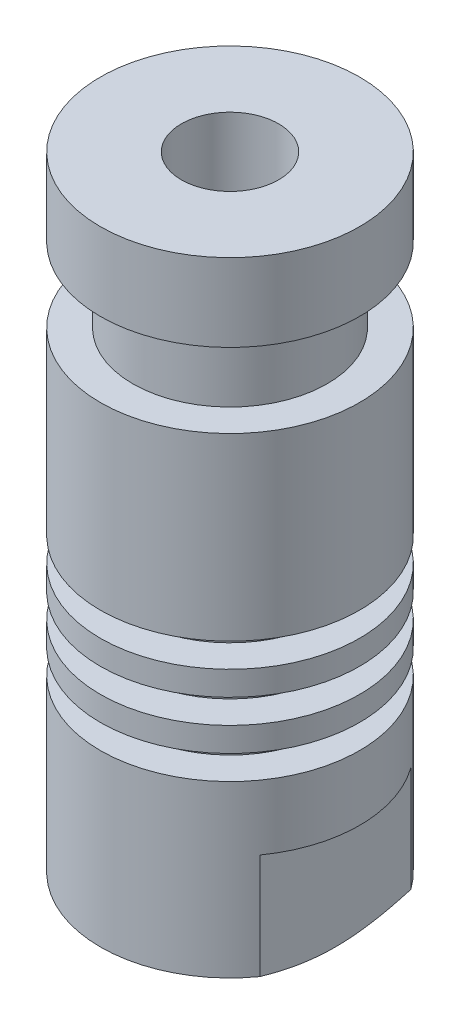
SolidWorks part; units mm, degrees
material "Gomma"
ref_plane "Piano frontale" through (0, 0, 0) normal (0, 0, 1) x (1, 0, 0)
ref_plane "Piano superiore" through (0, 0, 0) normal (0, 1, 0) x (1, 0, 0)
ref_plane "Piano destro" through (0, 0, 0) normal (1, 0, 0) x (0, 0, -1)
sketch "Schizzo1" plane through (0, 0, 0) normal (0, 0, 1) x (1, 0, 0)
  line L0 (0, 0) -> (-5, 0)
  line L1 (-5, 0) -> (-8, 1.5)
  line L2 (-8, 1.5) -> (-8, 12)
  line L3 (-8, 12) -> (-6, 12)
  line L4 (-6, 12) -> (-6, 13.5)
  line L5 (-6, 13.5) -> (-8, 13.5)
  line L6 (-8, 13.5) -> (-8, 15)
  line L7 (-8, 15) -> (-6, 15)
  line L8 (-6, 15) -> (-6, 16.5)
  line L9 (-6, 16.5) -> (-8, 16.5)
  line L10 (-8, 16.5) -> (-8, 18)
  line L11 (-8, 18) -> (-6, 18)
  line L12 (-6, 18) -> (-6, 19.5)
  line L13 (-6, 19.5) -> (-8, 19.5)
  line L14 (-8, 19.5) -> (-8, 30.6)
  line L15 (-8, 30.6) -> (-6, 30.6)
  line L16 (-6, 30.6) -> (-6, 35.2)
  line L17 (-6, 35.2) -> (-8, 35.2)
  line L18 (-8, 35.2) -> (-8, 40)
  line L19 (-8, 40) -> (0, 40)
  line L20 (0, 40) -> (0, 0)
  line L21 (0, 129.4074) -> (0, -17.2322) construction
  dimension "D1" = 1.5
  dimension "D2" = 16
  dimension "D3" = 2
  dimension "D4" = 40
  dimension "D5" = 12
  dimension "D6" = 4.8
  dimension "D7" = 4.6
  dimension "D8" = 1.5
  dimension "D9" = 6
  dimension "D10" = 10
revolve "Rivoluzione1" add sketch "Schizzo1" angle 360 about L21
sketch "Schizzo2" plane through (0, 0, 0) normal (0, 0, 1) x (1, 0, 0)
  line L0 (-8, 8) -> (-6.5, 8)
  line L1 (-6.5, 8) -> (-6.5, 0)
  line L2 (-6.5, 0) -> (-8, 0)
  line L3 (-8, 0) -> (-8, 8)
  line L4 (6.5, 8) -> (6.5, 0)
  line L5 (6.5, 0) -> (8, 0)
  line L6 (8, 0) -> (8, 8)
  line L7 (8, 8) -> (6.5, 8)
  line L8 (0, 0) -> (0, 9.0399) construction
  line L9 (-5, 0) -> (5, 0) construction
  line L10 (8, 40) -> (-8, 40) construction
  line L11 (8, 1.5) -> (8, 12) construction
  line L12 (-8, 12) -> (-8, 1.5) construction
  dimension "D1" = 32
  dimension "D2" = 1.5
extrude "Taglio-Estrusione1" cut sketch "Schizzo2" against normal up to next and the other way up to next
sketch "Schizzo7" plane through (0, 40, 0) normal (0, 1, 0) x (1, 0, 0)
  circle A0 centre (0, 0) radius 3
extrude "Taglio-Estrusione2" cut sketch "Schizzo7" against normal through all
hole_wizard "Foro filettato M8-1" positions "Schizzo9" profile "Schizzo8" tap size "M8" standard "ISO"
sketch "Schizzo9" plane through (0, 0, 0) normal (0, -1, 0) x (-1, 0, 0)
  point P0 (0, 0)
sketch "Schizzo8" plane through (0, 0, 0) normal (1, 0, 0) x (0, 0, -1)
  line L0 (0, 0) -> (0, 14.0429)
  line L1 (0, 14.0429) -> (3.4, 12)
  line L2 (3.4, 12) -> (3.4, 0)
  line L5 (3.4, 0) -> (0, 0)
  line L10 (0, 14.0429) -> (-3.4, 12) construction
  line L11 (0, -6.35) -> (0, 107.95) construction
  dimension "Tap Drill Dia." = 6.8
  dimension "Tap Drill Depth" = 12
  dimension "Drill Angle" = 118
cosmetic thread "Filettatura del foro3" parameters "D1"=12, "D2"=8
